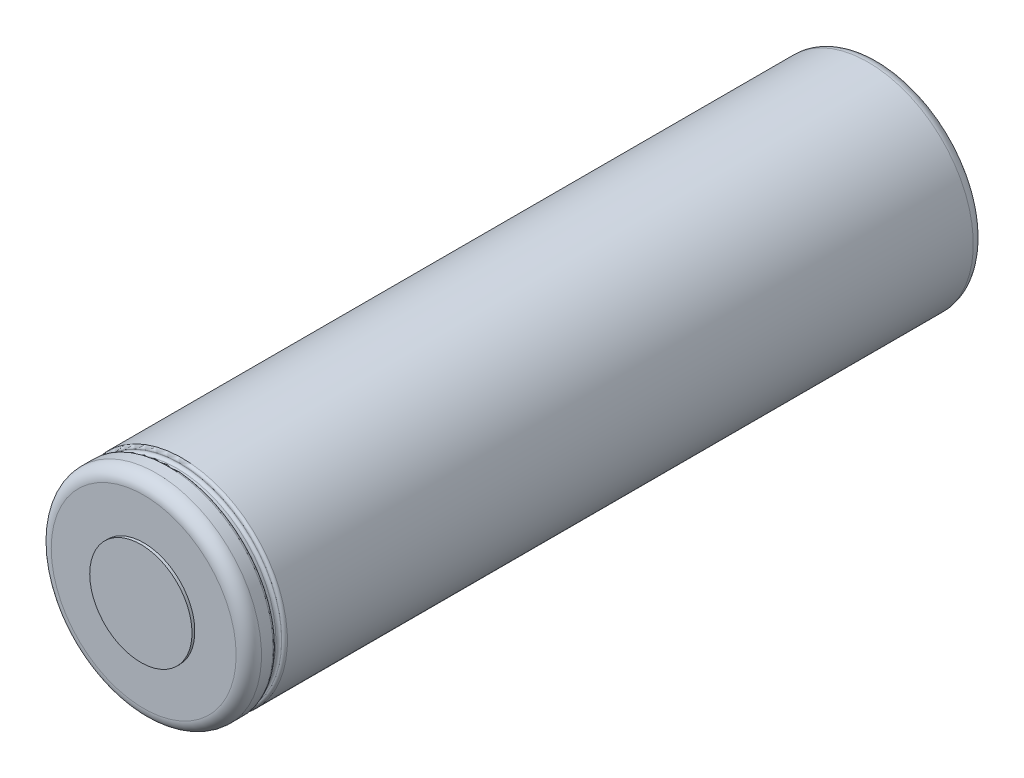
SolidWorks part; units mm, degrees
ref_plane "Front Plane" through (0, 0, 0) normal (0, 0, 1) x (1, 0, 0)
ref_plane "Top Plane" through (0, 0, 0) normal (0, 1, 0) x (1, 0, 0)
ref_plane "Right Plane" through (0, 0, 0) normal (1, 0, 0) x (0, 0, -1)
sketch "Sketch2" plane through (0, 0, 0) normal (1, 0, 0) x (0, 0, -1)
  line L0 (0, 0) -> (-65, 0)
  line L6 (-61.3538, 9.25) -> (-1, 9.25)
  line L7 (0, 8.25) -> (0, 0)
  line L8 (-63.6361, 9.25) -> (-62.6057, 9.25)
  line L9 (-62.3557, 9) -> (-62.3557, 8.9897)
  line L10 (-62.1057, 8.7397) -> (-61.8538, 8.7397)
  line L11 (-61.6038, 8.9897) -> (-61.6038, 9)
  line L12 (-64.75, 8.1361) -> (-64.75, 4.5)
  line L13 (-64.75, 4.5) -> (-65, 4.5)
  line L14 (-65, 4.5) -> (-65, 0)
  arc A0 (-1, 9.25) -> (0, 8.25) centre (-1, 8.25) cw
  arc A5 (-64.75, 8.1361) -> (-63.6361, 9.25) centre (-63.6361, 8.1361) cw
  arc A6 (-61.3538, 9.25) -> (-61.6038, 9) centre (-61.3538, 9) ccw
  arc A7 (-62.6057, 9.25) -> (-62.3557, 9) centre (-62.6057, 9) cw
  arc A8 (-62.1057, 8.7397) -> (-62.3557, 8.9897) centre (-62.1057, 8.9897) cw
  arc A9 (-61.8538, 8.7397) -> (-61.6038, 8.9897) centre (-61.8538, 8.9897) ccw
  dimension "D3" = 1
  dimension "D4" = 0.25
  dimension "D1" = 65
  dimension "D5" = 4.5
  dimension "D6" = 0.25
  dimension "D2" = 9.25
  dimension "D7" = 9.25
revolve "Revolve1" add sketch "Sketch2" angle 360 about L0
equation "\"D7@Sketch2\"=\"D2@Sketch2\""
